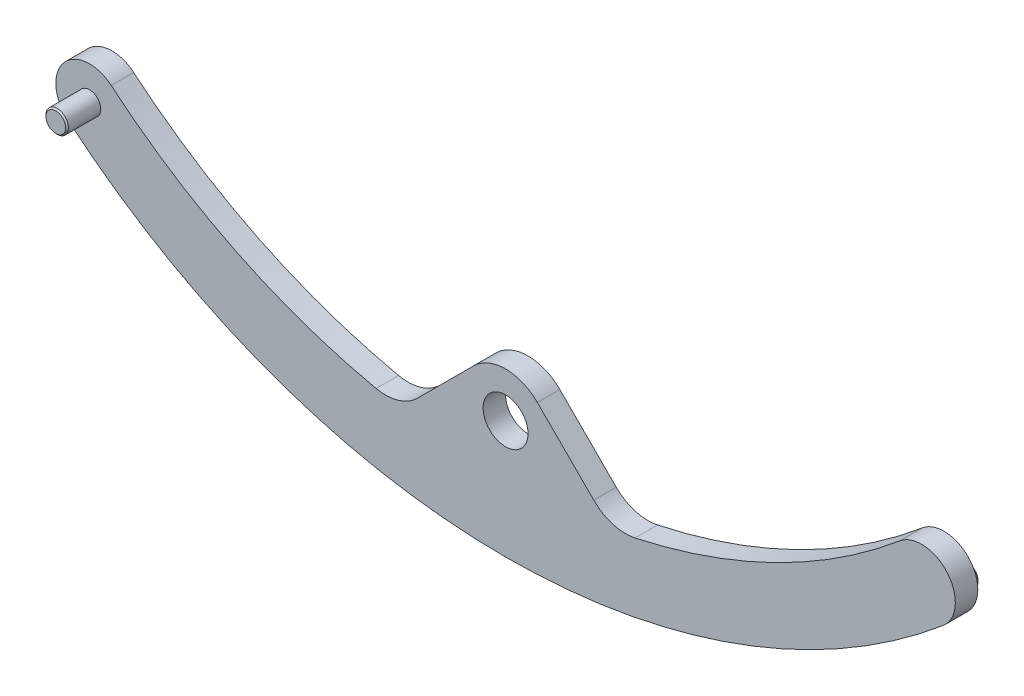
SolidWorks part; units mm, degrees
ref_plane "Front Plane" through (0, 0, 0) normal (0, 0, 1) x (1, 0, 0)
ref_plane "Top Plane" through (0, 0, 0) normal (0, 1, 0) x (1, 0, 0)
ref_plane "Right Plane" through (0, 0, 0) normal (1, 0, 0) x (0, 0, -1)
sketch "Sketch1" plane through (0, 0, 0) normal (0, 0, 1) x (1, 0, 0)
  line L0 (0, 0) -> (0, -15) construction
  line L1 (-5.6569, 5.6569) -> (-28.8292, -17.5154)
  line L2 (5.6569, 5.6569) -> (28.8292, -17.5154)
  circle A0 centre (0, 0) radius 4
  arc A1 (-74.0338, 12) -> (74.0338, 12) centre (0, 100) ccw construction
  arc A2 (-77.8964, 7.4087) -> (77.8964, 7.4087) centre (0, 100) ccw
  arc A3 (-70.1711, 16.5913) -> (70.1711, 16.5913) centre (0, 100) ccw
  arc A4 (-70.1711, 16.5913) -> (-77.8964, 7.4087) centre (-74.0338, 12) ccw
  arc A5 (77.8964, 7.4087) -> (70.1711, 16.5913) centre (74.0338, 12) ccw
  circle A6 centre (0, 0) radius 8
  point P7 (0, -15)
  dimension "D1" = 8
  dimension "D5" = 16
  dimension "D2" = 15
  dimension "D3" = 75
  dimension "D4" = 75
  dimension "D6" = 45
  dimension "D7" = 45
extrude "Boss-Extrude1" add sketch "Sketch1" along normal blind 4 contours A6 L1 A3 | A6 A3 A0 | A6 A3 L2 | A6 A3 A4 A2 A5
sketch "Sketch2" plane through (0, 0, 4) normal (0, 0, 1) x (1, 0, 0)
  circle A0 centre (-74.0338, 12) radius 2
  dimension "D1" = 4
extrude "Boss-Extrude2" add sketch "Sketch2" along normal blind 6
chamfer "Chamfer1" distance 0.25 angle 45 1 edges at (-72.0338, 12, 10)
sketch "Sketch3" plane through (0, 0, 0) normal (0, 0, -1) x (-1, 0, 0)
  circle A0 centre (-75.3213, 10.4696) radius 2
  dimension "D1" = 4
  dimension "D2" = 4
  dimension "D3" = 8
extrude "Boss-Extrude3" add sketch "Sketch3" along normal blind 3
chamfer "Chamfer2" distance 0.25 angle 45 1 edges at (73.3213, 10.4696, -3)
fillet "Fillet2" radius 8 2 edges at (-18.698, -7.3843, 2) (18.698, -7.3843, 2)
